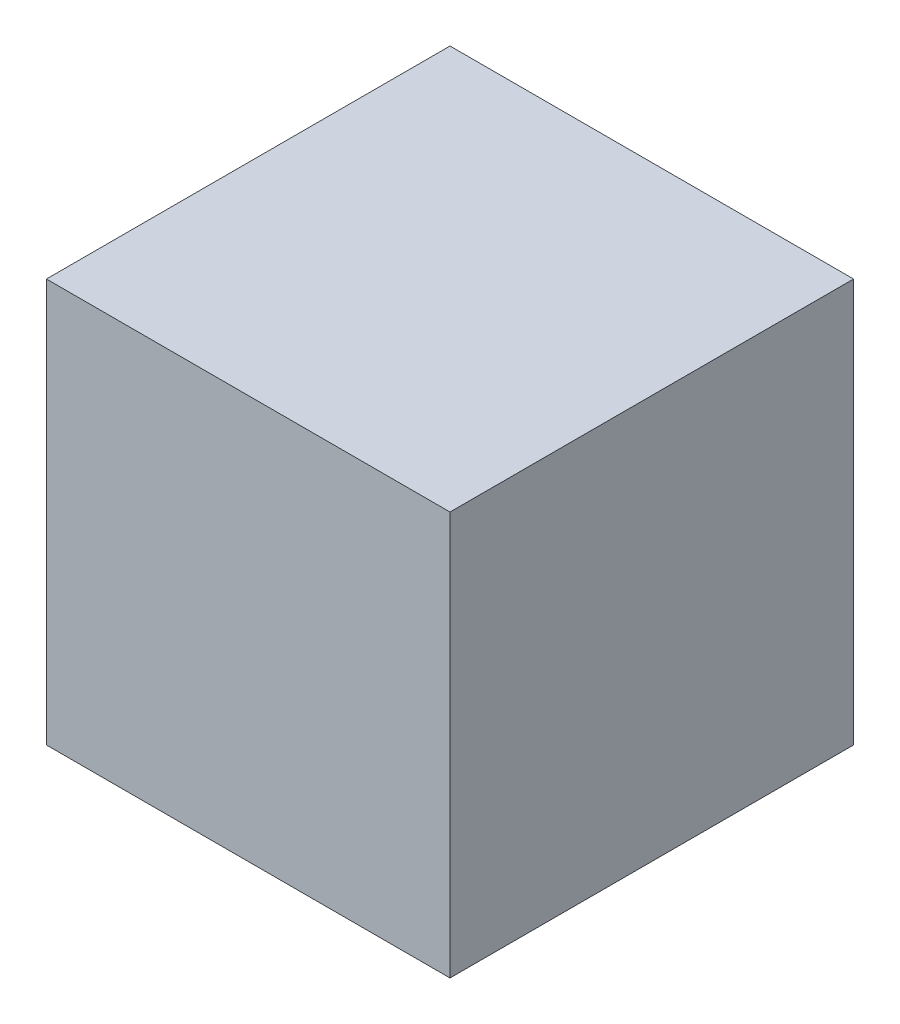
SolidWorks part; units mm, degrees
ref_plane "Alzado" through (0, 0, 0) normal (0, 0, 1) x (1, 0, 0)
ref_plane "Planta" through (0, 0, 0) normal (0, 1, 0) x (1, 0, 0)
ref_plane "Vista lateral" through (0, 0, 0) normal (1, 0, 0) x (0, 0, -1)
sketch3d "Croquis3D1" plane through (0, 0, 0) normal (0, 0, 1) x (1, 0, 0)
sketch "Croquis3" plane through (0, 0, 0) normal (0, 0, 1) x (1, 0, 0)
  line L1 (250, -250) -> (-250, -250)
  line L2 (250, -250) -> (250, 250)
  line L3 (250, 250) -> (-250, 250)
  line L4 (-250, -250) -> (-250, 250)
  line L5 (250, -250) -> (-250, 250) construction
  line L6 (250, 250) -> (-250, -250) construction
  point P0 (0, 0)
extrude "Saliente-Extruir1" add sketch "Croquis3" along normal blind 500
sketch "Croquis4" plane through (-250, 0, 0) normal (-1, 0, 0) x (0, 0, 1)
  line L0 (109.2375, 77.33) -> (386.5708, 77.33) construction
  line L1 (-514.5896, 101.8296) -> (309.4104, 101.8296) construction
  line L2 (183.4147, 76.0213) -> (333.4147, 76.0213) construction
sketch "Croquis5" plane through (0, 0, 500) normal (0, 0, 1) x (1, 0, 0)
  line L0 (-192.6514, -50.1782) -> (-99.3181, -50.1782) construction
  line L1 (7.3333, 35.5) -> (-21.0428, -109.5227) construction
  line L2 (-178.5928, -145.9993) -> (-149.2594, -145.9993) construction
  line L3 (-67.894, 19.2198) -> (8.7727, 19.2198) construction
  line L4 (-25.414, -142.0742) -> (4.586, -142.0742) construction
  line L5 (179.1781, 11.0829) -> (439.8448, 11.0829) construction
  line L6 (149.2098, -140.9779) -> (177.8765, -140.9779) construction
  line L7 (147.3596, 169.9696) -> (176.6929, 169.9696) construction
sketch "Croquis6" plane through (250, 0, 0) normal (1, 0, 0) x (0, 0, -1)
  line L0 (-161.5504, -89.692) -> (-108.2171, -89.692) construction
  line L1 (-372.4454, -53.9578) -> (-33.7788, -53.9578) construction
sketch "Croquis7" plane through (0, 0, 0) normal (0, 0, -1) x (-1, 0, 0)
  line L0 (-222.3439, -101.1788) -> (-175.0105, -101.1788) construction
  line L1 (-147.7178, 47.3131) -> (-98.3845, 47.3131) construction
  line L2 (155.19, 20.8706) -> (191.8567, 20.8706) construction
  line L3 (-103.6738, 196.1993) -> (-75.0072, 196.1993) construction
  line L4 (-117.2107, -217.7237) -> (-87.8774, -217.7237) construction
sketch "Croquis8" plane through (0, -250, 0) normal (0, -1, 0) x (1, 0, 0)
  line L0 (10.1113, 249.4245) -> (149.4447, 249.4245) construction
  line L1 (-122.1676, 439.394) -> (-92.8342, 439.394) construction
  line L2 (-9.9081, 436.2251) -> (18.7586, 436.2251) construction
  line L3 (95.3715, 448.2637) -> (125.3715, 448.2637) construction
sketch "Croquis9" plane through (0, 250, 0) normal (0, 1, 0) x (1, 0, 0)
  line L0 (-1173.8114, 1246.0292) -> (-1296.5444, 354.437) construction
  line L1 (397.0601, -511.9571) -> (214.0601, -555.3449) construction
  line L2 (74.5495, -10.2442) -> (435.8829, -10.2442) construction
  line L3 (7.3333, 35.5) -> (36.6667, 35.5) construction
  line L4 (-175.3575, -183.3335) -> (-175.3575, -212.6668) construction
  line L5 (-168.1727, -296.8055) -> (-168.1727, -326.8055) construction
  line L6 (-170.1387, -407.5693) -> (-170.1387, -434.9027) construction
  line L7 (174.2141, -60.5509) -> (174.2141, -89.8842) construction
  line L8 (166.7859, -172.4594) -> (166.7859, -202.4594) construction
  line L9 (169.2859, -282.5319) -> (169.2859, -311.1986) construction
  dimension "D1" = 900
